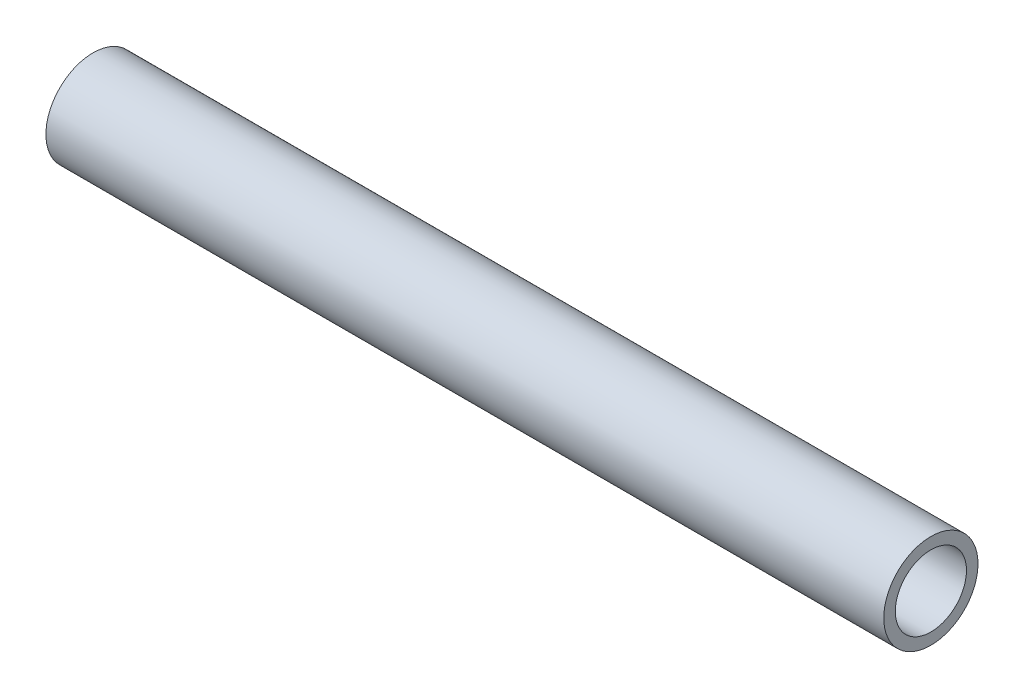
SolidWorks part; units mm, degrees
ref_plane "Front Plane" through (0, 0, 0) normal (0, 0, 1) x (1, 0, 0)
ref_plane "Top Plane" through (0, 0, 0) normal (0, 1, 0) x (1, 0, 0)
ref_plane "Right Plane" through (0, 0, 0) normal (1, 0, 0) x (0, 0, -1)
sketch "Sketch1" plane through (0, 0, 0) normal (1, 0, 0) x (0, 0, -1)
  circle A0 centre (0, 0) radius 28.575
  circle A1 centre (0, 0) radius 21.59
  dimension "D1" = 57.15
  dimension "D2" = 43.18
extrude "Boss-Extrude1" add sketch "Sketch1" along normal mid plane 508
